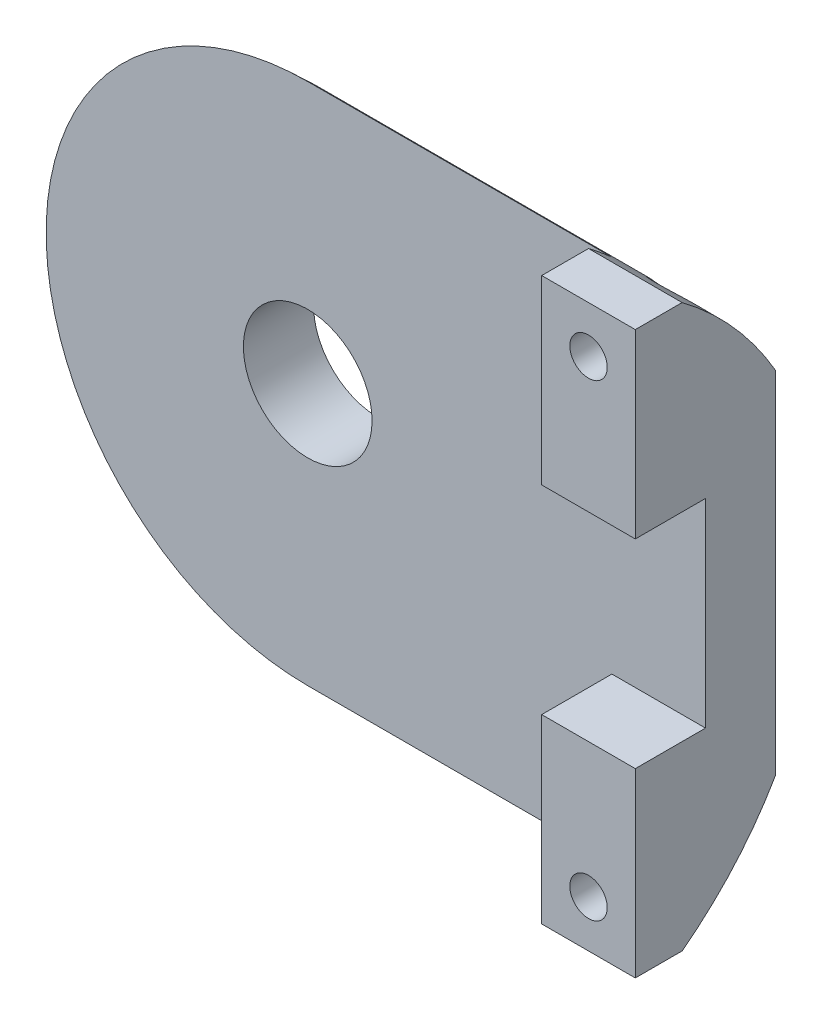
SolidWorks part; units mm, degrees
ref_plane "Front" through (0, 0, 0) normal (0, 0, 1) x (1, 0, 0)
ref_plane "Top" through (0, 0, 0) normal (0, 1, 0) x (1, 0, 0)
ref_plane "Right" through (0, 0, 0) normal (1, 0, 0) x (0, 0, -1)
sketch "Sketch1" plane through (0, 0, 0) normal (0, 0, 1) x (1, 0, 0)
  line L0 (13, 0) -> (17, 0) construction
  line L1 (17, 0) -> (17, 12)
  line L2 (17, 0) -> (17, -12)
  line L3 (0, 0) -> (38, 0) construction
  line L4 (17, 12) -> (5, 12)
  line L6 (17, -12) -> (5, -12)
  circle A0 centre (0, 0) radius 13
  circle A2 centre (0, 0) radius 2.75
extrude "Boss-Extrude1" add sketch "Sketch1" along normal blind 6
sketch "Sketch2" plane through (0, 0, 0) normal (0, 0, 1) x (1, 0, 0)
  line L0 (0, 13) -> (13, 13)
  line L1 (13, 0) -> (13, 4.25) construction
  line L2 (13, 0) -> (13, -4.25) construction
  line L3 (13, 13) -> (13, 0)
  line L4 (13, 4.25) -> (17, 4.25)
  line L5 (13, 0) -> (13, -13)
  line L6 (17, 12) -> (17, -12) construction
  line L7 (13, -13) -> (0, -13)
  line L8 (17, 4.25) -> (17, -4.25)
  line L9 (17, -4.25) -> (13, -4.25)
  circle A0 centre (0, 0) radius 13
extrude "Body Hole" cut sketch "Sketch2" along normal blind 3 from offset 3
sketch "Sketch3" plane through (0, 0, 0) normal (1, 0, 0) x (0, 0, -1)
  line L0 (0, 0) -> (-13, 0) construction
  line L1 (0, 0) -> (2, 0) construction
  line L2 (-13, 15) -> (2, 15)
  line L3 (2, 15) -> (2, 0)
  line L4 (2, 0) -> (2, -15)
  line L5 (2, -15) -> (-13, -15)
  circle A0 centre (-13, 0) radius 15
extrude "Cut-Extrude2" cut sketch "Sketch3" along normal through all
sketch "Sketch6" plane through (0, 0, 0) normal (1, 0, 0) x (0, 0, -1)
  line L0 (0, 0) -> (-13, 0) construction
  line L1 (0, 0) -> (2, 0) construction
  line L2 (-13, 15) -> (2, 15)
  line L3 (2, 15) -> (2, 0)
  line L4 (2, 0) -> (2, 15)
  line L5 (2, 15) -> (-13, 15)
  line L6 (2, 15) -> (1, 15)
  line L8 (1, 5.3852) -> (2, 5.3852)
  circle A0 centre (-13, 0) radius 15
revolve "Cut-Revolve1" cut sketch "Sketch6" angle 180 about L0
sketch "Sketch7" plane through (0, 0, 0) normal (0, 0, 1) x (1, 0, 0)
  line L0 (17, 0) -> (13, 0) construction
  line L4 (15, 0) -> (15, 10) construction
  line L5 (15, 0) -> (15, -10) construction
  circle A0 centre (15, 10) radius 0.8
  circle A1 centre (15, -10) radius 0.8
extrude "Screw Holes" cut sketch "Sketch7" along normal through all
sketch "Sketch9" plane through (0, 0, 0) normal (0, 0, 1) x (1, 0, 0)
  circle A0 centre (15, 10) radius 1.25
extrude "Screw Heads" cut sketch "Sketch9" along normal blind 4
